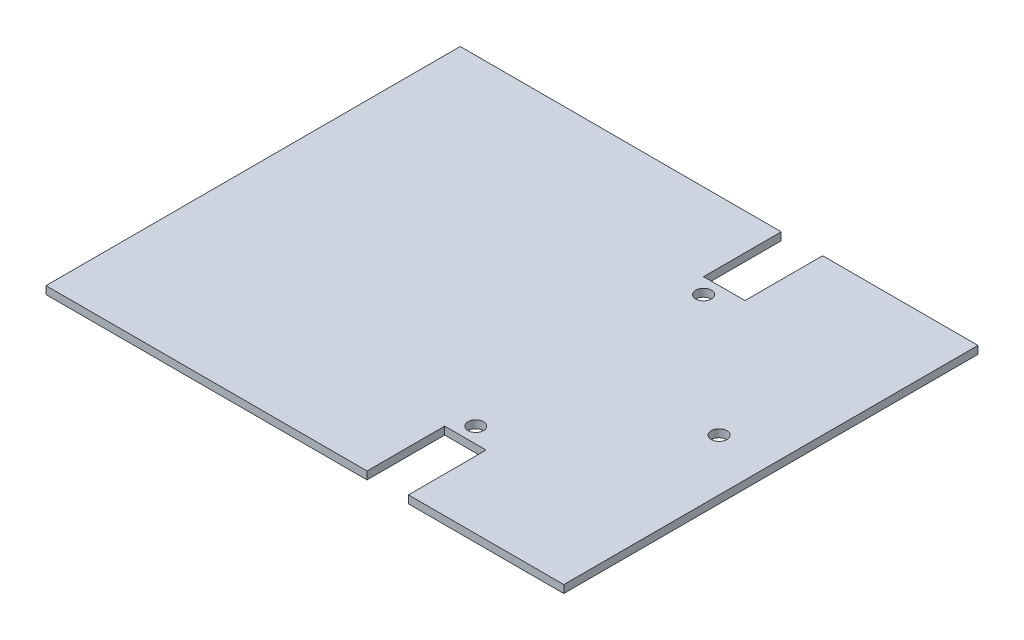
SolidWorks part; units mm, degrees
ref_plane "Front Plane" through (0, 0, 0) normal (0, 0, 1) x (1, 0, 0)
ref_plane "Top Plane" through (0, 0, 0) normal (0, 1, 0) x (1, 0, 0)
ref_plane "Right Plane" through (0, 0, 0) normal (1, 0, 0) x (0, 0, -1)
sketch "Sketch1" plane through (0, 0, 0) normal (0, 1, 0) x (1, 0, 0)
  line L1 (0, 0) -> (100, 0)
  line L2 (0, 0) -> (0, 80)
  line L3 (0, 80) -> (100, 80)
  line L4 (100, 0) -> (100, 80)
  dimension "D1" = 80
  dimension "D2" = 100
extrude "Boss-Extrude1" add sketch "Sketch1" along normal blind 1.5
sketch "Sketch2" plane through (0, 1.5, 0) normal (0, 1, 0) x (1, 0, 0)
  line L0 (100, 80) -> (0, 80) construction
  line L1 (62, 80) -> (70, 80)
  line L2 (62, 80) -> (62, 65)
  line L3 (62, 65) -> (70, 65)
  line L4 (70, 80) -> (70, 65)
  line L5 (0, 0) -> (100, 0) construction
  line L6 (62, 0) -> (70, 0)
  line L7 (62, 0) -> (62, 15)
  line L8 (62, 15) -> (70, 15)
  line L9 (70, 0) -> (70, 15)
  line L10 (100, 0) -> (100, 80) construction
  dimension "D1" = 30
  dimension "D2" = 15
  dimension "D3" = 8
extrude "Cut-Extrude1" cut sketch "Sketch2" against normal up to next
sketch "Sketch3" plane through (0, 1.5, 0) normal (0, 1, 0) x (1, 0, 0)
  line L0 (62, 15) -> (62, 0) construction
  line L1 (70, 0) -> (100, 0) construction
  line L3 (100, 0) -> (100, 80) construction
  line L4 (70, 15) -> (62, 15) construction
  line L5 (62, 65) -> (70, 65) construction
  circle A0 centre (65, 62) radius 1.5
  circle A1 centre (90, 40) radius 1.5
  circle A2 centre (65, 18) radius 1.5
  dimension "D1" = 40
  dimension "D2" = 3
  dimension "D3" = 3
  dimension "D4" = 10
  dimension "D5" = 3
  dimension "D6" = 3
extrude "Cut-Extrude2" cut sketch "Sketch3" against normal up to next
